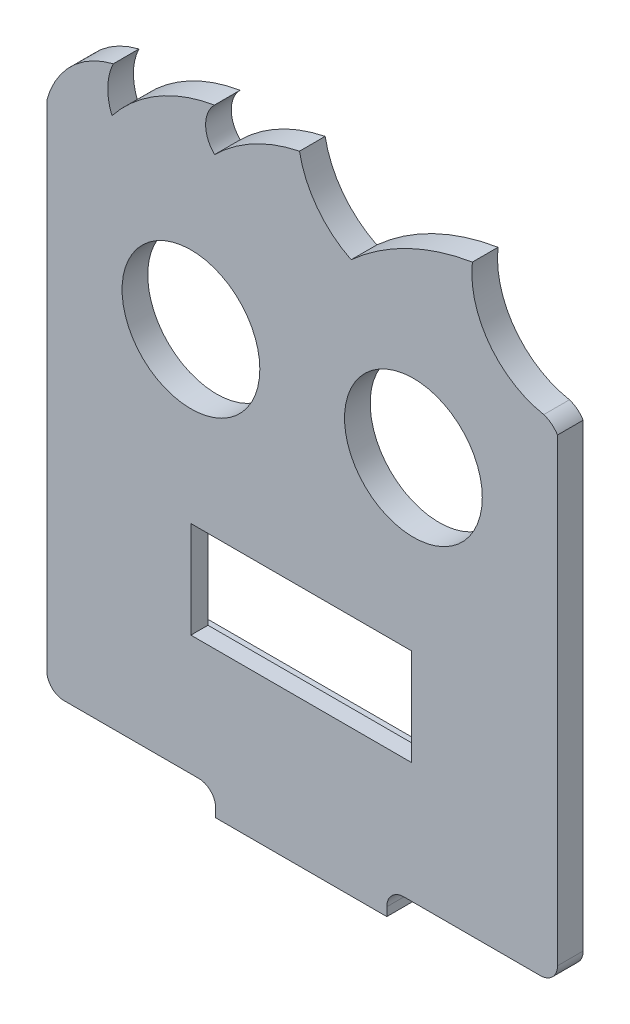
SolidWorks part; units mm, degrees
ref_plane "Alzado" through (0, 0, 0) normal (0, 0, 1) x (1, 0, 0)
ref_plane "Planta" through (0, 0, 0) normal (0, 1, 0) x (1, 0, 0)
ref_plane "Vista lateral" through (0, 0, 0) normal (1, 0, 0) x (0, 0, -1)
sketch "Model" plane through (0, 0, 0) normal (0, 0, 1) x (1, 0, 0)
  line L0 (73.4898, -38.9769) -> (73.4898, -27.6769)
  line L1 (73.4898, -27.6769) -> (47.6898, -27.6769)
  line L2 (47.6898, -27.6769) -> (47.6898, -38.9769)
  line L3 (47.6898, -38.9769) -> (73.4898, -38.9769)
  line L4 (50.5898, -56.021) -> (70.5898, -56.021)
  line L5 (60.5898, -38.9769) -> (60.5898, -56.021) construction
  line L6 (32.8533, -53.021) -> (48.5898, -53.021)
  line L7 (88.5423, -53.021) -> (72.5898, -53.021)
  line L8 (50.5898, -55.021) -> (50.5898, -56.021)
  line L9 (70.5898, -55.021) -> (70.5898, -56.021)
  line L50 (30.8533, 6.7762) -> (30.8533, -51.021)
  line L51 (90.5423, -51.021) -> (90.5423, 2.7067)
  circle A0 centre (47.699, -8.021) radius 8.05
  circle A1 centre (73.699, -8.021) radius 8.05
  arc A2 (50.5898, -55.021) -> (48.5898, -53.021) centre (48.5898, -55.021) ccw
  arc A3 (72.5898, -53.021) -> (70.5898, -55.021) centre (72.5898, -55.021) ccw
  arc A31 (30.8533, -51.021) -> (32.8533, -53.021) centre (32.8533, -51.021) ccw
  arc A32 (38.616, 14.3189) -> (30.8533, 6.7762) centre (41.1224, 3.9735) ccw
  arc A33 (38.616, 14.3189) -> (38.469, 8.9961) centre (44.491, 11.4932) ccw
  arc A34 (50.4366, 16.0514) -> (38.469, 8.9961) centre (53.6246, -3.0341) ccw
  arc A35 (50.4366, 16.0514) -> (50.4597, 11.0514) centre (52.9481, 13.5629) ccw
  arc A36 (60.3852, 16.3614) -> (50.4597, 11.0514) centre (64.3778, -3.0332) ccw
  arc A37 (60.3852, 16.3614) -> (66.422, 8.3891) centre (71.3759, 18.4121) ccw
  arc A38 (80.5902, 15.2365) -> (66.422, 8.3891) centre (85.1678, -12.3168) ccw
  arc A39 (80.5902, 15.2365) -> (88.9383, 3.9735) centre (90.8356, 14.1051) ccw
  arc A40 (90.5423, 2.7067) -> (88.9383, 3.9735) centre (87.9922, 1.1265) ccw
  arc A41 (88.5423, -53.021) -> (90.5423, -51.021) centre (88.5423, -51.021) ccw
  dimension "D1" = 20
  dimension "D2" = 2
extrude "Saliente-Extruir1" add sketch "Model" along normal blind 3
sketch "Croquis2" plane through (0, 0, 0) normal (0, 0, -1) x (-1, 0, 0)
  line L0 (-70.5898, -56.021) -> (-70.5898, -53.021)
  line L1 (-70.5898, -53.021) -> (-50.5898, -53.021)
  line L2 (-50.5898, -53.021) -> (-50.5898, -56.021)
  line L3 (-50.5898, -56.021) -> (-70.5898, -56.021)
  dimension "D1" = 3
extrude "Saliente-Extruir2" add sketch "Croquis2" along normal blind 8
sketch "Croquis3" plane through (0, -53.021, 0) normal (0, 1, 0) x (1, 0, 0)
  line L0 (60.5898, 8) -> (60.5898, 0) construction
  line L1 (50.5898, 8) -> (70.5898, 8) construction
  line L2 (50.5898, 0) -> (70.5898, 0) construction
  circle A0 centre (66.5898, 3.5) radius 1.5
  circle A1 centre (54.5898, 3.5) radius 1.5
  dimension "D1" = 6
  dimension "D2" = 3.5
extrude "Cortar-Extruir1" cut sketch "Croquis3" against normal blind 3
sketch "Croquis4" plane through (0, -53.021, 0) normal (0, 1, 0) x (1, 0, 0)
  circle A0 centre (66.5898, 3.5) radius 2.25
  circle A1 centre (54.5898, 3.5) radius 2.25
extrude "Cortar-Extruir2" cut sketch "Croquis4" against normal blind 1
fillet "Redondeo1" radius 2 2 edges at (50.5898, -54.521, -8) (70.5898, -54.521, -8)
sketch "Croquis5" plane through (0, 0, 0) normal (0, 0, -1) x (-1, 0, 0)
  line L0 (-80.9398, -27.2769) -> (-42.6398, -27.2769)
  line L1 (-42.6398, -27.2769) -> (-42.6398, -39.3769)
  line L2 (-42.6398, -39.3769) -> (-80.9398, -39.3769)
  line L3 (-80.9398, -39.3769) -> (-80.9398, -27.2769)
  line L4 (-73.4898, -27.6769) -> (-47.6898, -27.6769) construction
  line L5 (-47.6898, -27.6769) -> (-47.6898, -38.9769) construction
  point P4 (-42.2571, -27.132)
  point P5 (-42.5466, -27.2426)
  point P6 (0, 0)
  point P7 (-42.5932, -39.407)
  point P8 (-80.9613, -39.3885)
  point P9 (0, 0)
  point P10 (-80.9653, -27.2574)
  dimension "D1" = 38.3
  dimension "D2" = 12.1
  dimension "D3" = 0.4
  dimension "D4" = 5.05
extrude "Cortar-Extruir3" cut sketch "Croquis5" against normal blind 1
